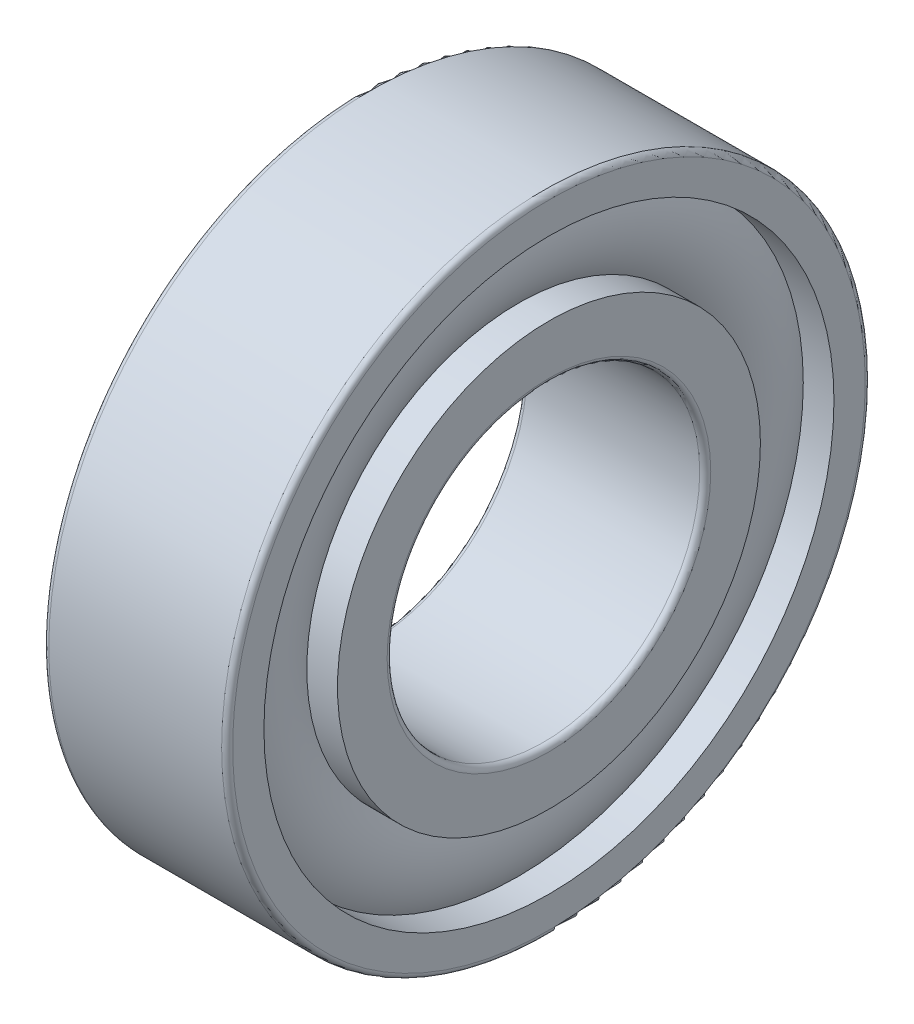
SolidWorks part; units mm, degrees
ref_plane "Front Plane" through (0, 0, 0) normal (0, 0, 1) x (1, 0, 0)
ref_plane "Top Plane" through (0, 0, 0) normal (0, 1, 0) x (1, 0, 0)
ref_plane "Right Plane" through (0, 0, 0) normal (1, 0, 0) x (0, 0, -1)
sketch "Sketch1" plane through (0, 0, 0) normal (0, 0, 1) x (1, 0, 0)
  line L0 (2.6509, 15.5) -> (4.3196, 15.5)
  line L1 (2.9509, 8.5) -> (12.3509, 8.5)
  line L2 (2.6509, 8.8) -> (2.6509, 11.5)
  line L3 (2.6509, 11.5) -> (4.3196, 11.5)
  line L4 (12.6509, 8.8) -> (12.6509, 11.5)
  line L9 (12.6509, 15.5) -> (12.6509, 17.2)
  line L10 (12.3509, 17.5) -> (2.9509, 17.5)
  line L11 (2.6509, 17.2) -> (2.6509, 15.5)
  line L12 (7.6509, 15.1447) -> (7.6509, 11.8553) construction
  line L13 (10.9822, 15.5) -> (12.6509, 15.5)
  line L14 (10.9822, 11.5) -> (12.6509, 11.5)
  arc A0 (12.3509, 8.5) -> (12.6509, 8.8) centre (12.3509, 8.8) ccw
  arc A1 (2.9509, 8.5) -> (2.6509, 8.8) centre (2.9509, 8.8) cw
  arc A2 (12.6509, 17.2) -> (12.3509, 17.5) centre (12.3509, 17.2) ccw
  arc A3 (2.9509, 17.5) -> (2.6509, 17.2) centre (2.9509, 17.2) ccw
  arc A4 (4.3196, 15.5) -> (4.3196, 11.5) centre (7.6509, 13.5) ccw
  arc A5 (10.9822, 11.5) -> (10.9822, 15.5) centre (7.6509, 13.5) ccw
  point P6 (12.6509, 8.5)
  point P9 (2.6509, 8.5)
  point P27 (7.6509, 8.5)
  point P28 (7.6509, 17.5)
  dimension "D4" = 0.3
  dimension "D5" = 0.3
  dimension "D1" = 8.5
  dimension "D2" = 10
  dimension "D3" = 11.5
  dimension "D6" = 15.5
  dimension "D7" = 17.5
ref_axis "Axis1" through (14.7, 0, 0) along (-1, 0, 0)
revolve "Revolve1" add sketch "Sketch1" angle 360 about axis through (14.7, 0, 0) along (-1, 0, 0)
